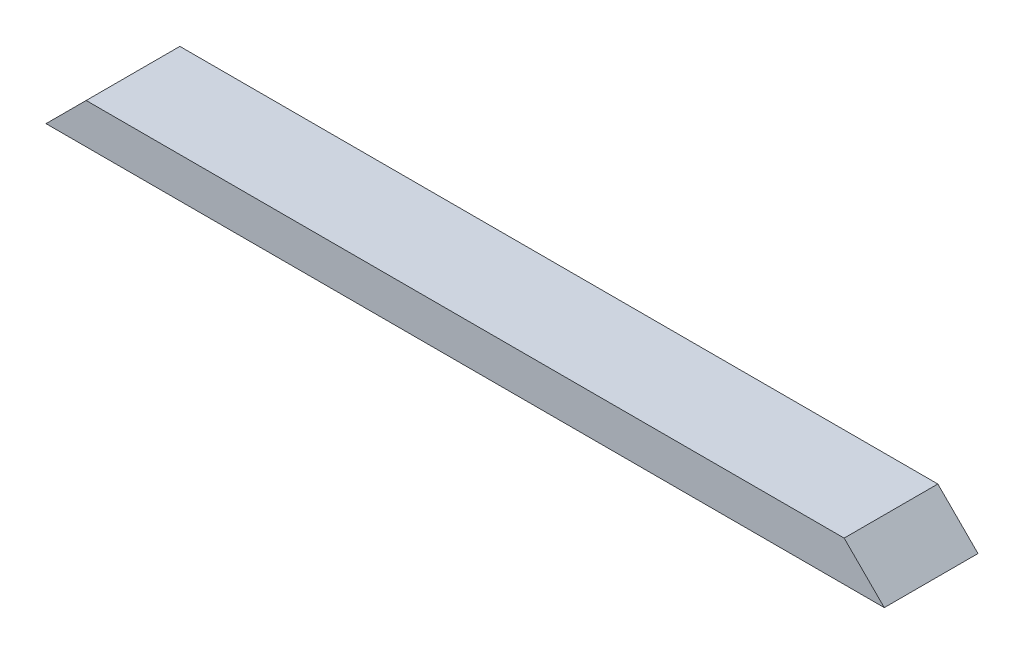
SolidWorks part; units mm, degrees
material "Pine"
ref_plane "Front Plane" through (0, 0, 0) normal (0, 0, 1) x (1, 0, 0)
ref_plane "Top Plane" through (0, 0, 0) normal (0, 1, 0) x (1, 0, 0)
ref_plane "Right Plane" through (0, 0, 0) normal (1, 0, 0) x (0, 0, -1)
sketch "Sketch1" plane through (0, 0, 0) normal (0, 1, 0) x (1, 0, 0)
  line L1 (0, 0) -> (795.3756, 0)
  line L2 (0, 0) -> (0, 88.9)
  line L3 (0, 88.9) -> (795.3756, 88.9)
  line L4 (795.3756, 0) -> (795.3756, 88.9)
  dimension "D1" = 88.9
  dimension "D2" = 795.3756
extrude "Boss-Extrude1" add sketch "Sketch1" along normal blind 38.1
sketch "Sketch2" plane through (0, 0, 0) normal (0, 0, 1) x (1, 0, 0)
  line L0 (0, 0) -> (38.1, 38.1)
  line L1 (0, 38.1) -> (795.3756, 38.1) construction
  line L2 (38.1, 38.1) -> (0, 38.1)
  line L3 (0, 38.1) -> (0, 0)
  line L5 (795.3756, 0) -> (795.3756, 38.1)
  line L9 (795.3756, 38.1) -> (757.2756, 38.1)
  line L10 (757.2756, 38.1) -> (795.3756, 0)
  dimension "D1" = 38.1
  dimension "D2" = 38.1
  dimension "D3" = 38.1
extrude "Cut-Extrude1" cut sketch "Sketch2" against normal through all
